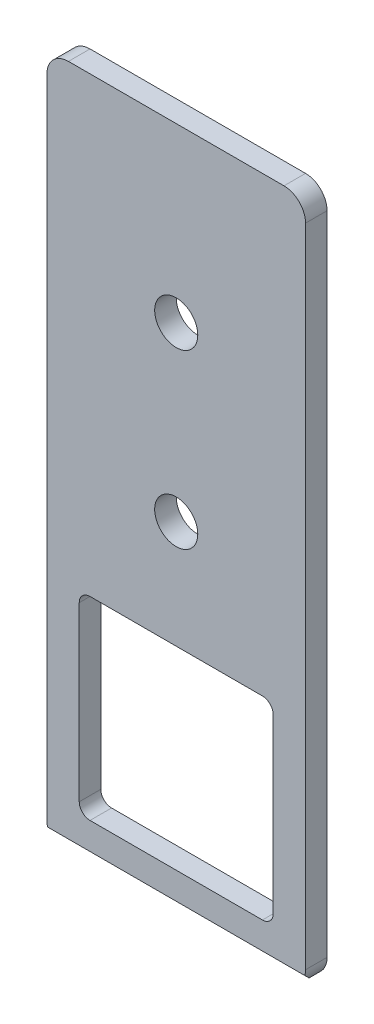
SolidWorks part; units mm, degrees
ref_plane "Front Plane" through (0, 0, 0) normal (0, 0, 1) x (1, 0, 0)
ref_plane "Top Plane" through (0, 0, 0) normal (0, 1, 0) x (1, 0, 0)
ref_plane "Right Plane" through (0, 0, 0) normal (1, 0, 0) x (0, 0, -1)
sketch "Sketch1" plane through (0, 0, 0) normal (0, 0, 1) x (1, 0, 0)
  line L0 (19.05, 101.6) -> (19.05, 0) construction
  line L1 (3.175, 0) -> (34.925, 0)
  line L2 (0, 3.175) -> (0, 98.425)
  line L3 (3.175, 101.6) -> (34.925, 101.6)
  line L4 (38.1, 3.175) -> (38.1, 98.425)
  line L5 (6.35, 6.35) -> (31.75, 6.35)
  line L6 (4.7625, 7.9375) -> (4.7625, 33.3375)
  line L7 (6.35, 34.925) -> (31.75, 34.925)
  line L8 (33.3375, 7.9375) -> (33.3375, 33.3375)
  circle A0 centre (19.05, 50.8) radius 3.175
  circle A1 centre (19.05, 76.2) radius 3.175
  arc A2 (6.35, 6.35) -> (4.7625, 7.9375) centre (6.35, 7.9375) cw
  arc A3 (31.75, 6.35) -> (33.3375, 7.9375) centre (31.75, 7.9375) ccw
  arc A4 (31.75, 34.925) -> (33.3375, 33.3375) centre (31.75, 33.3375) cw
  arc A5 (4.7625, 33.3375) -> (6.35, 34.925) centre (6.35, 33.3375) cw
  arc A6 (0, 98.425) -> (3.175, 101.6) centre (3.175, 98.425) cw
  arc A7 (34.925, 101.6) -> (38.1, 98.425) centre (34.925, 98.425) cw
  arc A8 (34.925, 0) -> (38.1, 3.175) centre (34.925, 3.175) ccw
  arc A9 (3.175, 0) -> (0, 3.175) centre (3.175, 3.175) cw
  point P17 (4.7625, 6.35)
  point P20 (33.3375, 6.35)
  point P23 (33.3375, 34.925)
  point P28 (0, 101.6)
  point P31 (38.1, 101.6)
  point P36 (0, 0)
  dimension "D7" = 6.35
  dimension "D8" = 6.35
  dimension "D11" = 1.5875
  dimension "D12" = 3.175
  dimension "D1" = 38.1
  dimension "D2" = 101.6
  dimension "D3" = 28.575
  dimension "D4" = 4.7625
  dimension "D5" = 6.35
  dimension "D6" = 28.575
  dimension "D9" = 25.4
  dimension "D10" = 25.4
extrude "Boss-Extrude1" add sketch "Sketch1" along normal blind 3.175
sketch "Sketch2" plane through (0, 0, 0) normal (-1, 0, 0) x (0, 0, 1)
  line L0 (0.7938, 0) -> (3.175, 2.3813)
  line L1 (3.175, 0) -> (0, 0) construction
  line L2 (3.175, 0) -> (3.175, 3.175) construction
  line L3 (0.7938, 0) -> (3.175, 0)
  line L4 (3.175, 0) -> (3.175, 2.3813)
  dimension "D1" = 45
  dimension "D2" = 2.3813
extrude "Cut-Extrude1" cut sketch "Sketch2" against normal blind 85.471
